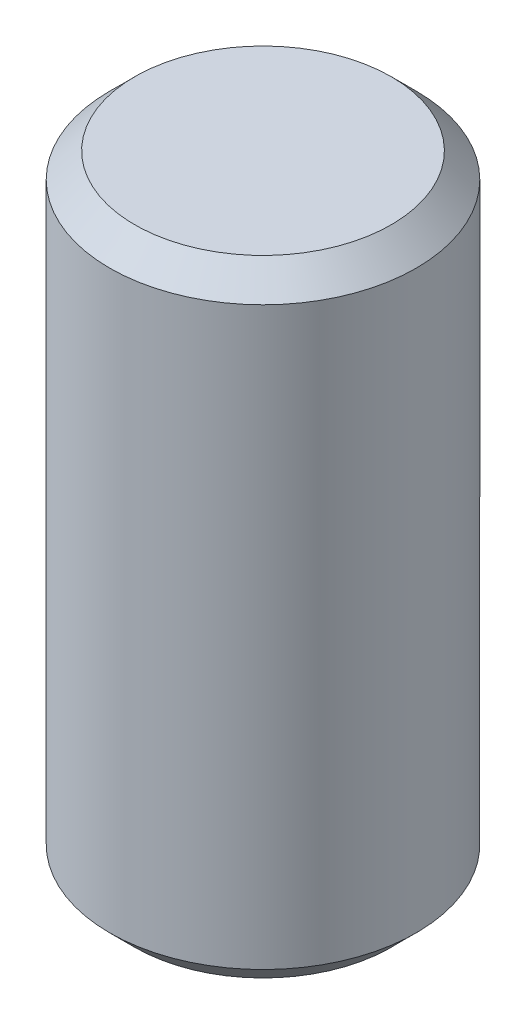
SolidWorks part; units mm, degrees
ref_plane "Front" through (0, 0, 0) normal (0, 0, 1) x (1, 0, 0)
ref_plane "Top" through (0, 0, 0) normal (0, 1, 0) x (1, 0, 0)
ref_plane "Right" through (0, 0, 0) normal (1, 0, 0) x (0, 0, -1)
sketch "Sketch1" plane through (0, 0, 0) normal (0, 0, 1) x (1, 0, 0)
  line L0 (0, 6.0802) -> (0, -6.0802) construction
  line L1 (0, -6.35) -> (3.1115, -6.35)
  line L2 (3.1115, -6.35) -> (3.1115, 6.35)
  line L3 (3.1115, 6.35) -> (0, 6.35)
  line L4 (0, 6.35) -> (0, -6.35)
  point P6 (0, 0)
  dimension "D1" = 6.223
  dimension "D2" = 12.7
revolve "Revolve1" add sketch "Sketch1" angle 360 about L0
chamfer "Chamfer1" distance 0.508 angle 45 2 edges at (0, -6.35, 3.1115) (0, 6.35, 3.1115)
